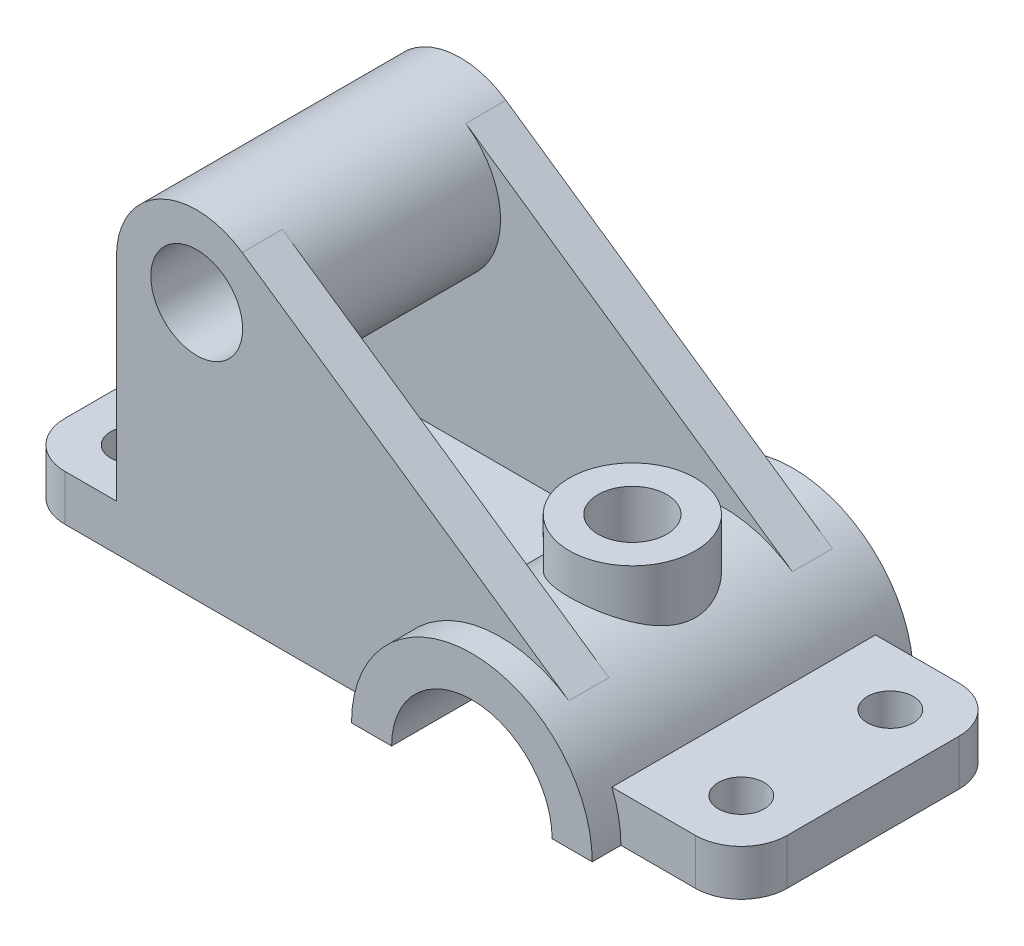
SolidWorks part; units mm, degrees
material "AISI 304"
ref_plane "Front Plane" through (0, 0, 0) normal (0, 0, 1) x (1, 0, 0)
ref_plane "Top Plane" through (0, 0, 0) normal (0, 1, 0) x (1, 0, 0)
ref_plane "Right Plane" through (0, 0, 0) normal (1, 0, 0) x (0, 0, -1)
sketch "Sketch1" plane through (0, 0, 0) normal (0, 1, 0) x (1, 0, 0)
  line L1 (55, -23) -> (-55, -23)
  line L2 (63, -15) -> (63, 15)
  line L3 (55, 23) -> (-55, 23)
  line L4 (-63, -15) -> (-63, 15)
  line L5 (63, -23) -> (-63, 23) construction
  line L6 (63, 23) -> (-63, -23) construction
  line L7 (-53, -13) -> (53, -13) construction
  line L8 (-53, -13) -> (-53, 13) construction
  line L9 (-53, 13) -> (53, 13) construction
  line L10 (53, -13) -> (53, 13) construction
  line L11 (-53, -13) -> (53, 13) construction
  line L12 (-53, 13) -> (53, -13) construction
  arc A0 (-63, -15) -> (-55, -23) centre (-55, -15) ccw
  arc A1 (63, -15) -> (55, -23) centre (55, -15) cw
  arc A2 (63, 15) -> (55, 23) centre (55, 15) ccw
  arc A3 (-55, 23) -> (-63, 15) centre (-55, 15) ccw
  circle A4 centre (-53, 13) radius 4
  circle A5 centre (53, 13) radius 4
  circle A6 centre (-53, -13) radius 4
  circle A7 centre (53, -13) radius 4
  point P0 (0, 0)
  point P18 (0, 0)
  dimension "D3" = 8
  dimension "D6" = 8
  dimension "D1" = 46
  dimension "D2" = 126
  dimension "D4" = 26
  dimension "D5" = 106
extrude "Boss-Extrude1" add sketch "Sketch1" along normal blind 8
sketch "Sketch2" plane through (0, 0, 23) normal (0, 0, 1) x (1, 0, 0)
  line L0 (-55, 0) -> (55, 0) construction
  line L1 (63, 8) -> (63, 0) construction
  line L2 (0, 0) -> (42, 0)
  arc A0 (42, 0) -> (0, 0) centre (21, 0) ccw
  point P4 (63, 4)
  dimension "D1" = 42
  dimension "D2" = 42
extrude "Boss-Extrude2" add sketch "Sketch2" against normal blind 51 and the other way blind 5
sketch "Sketch3" plane through (0, 0, 23) normal (0, 0, 1) x (1, 0, 0)
  line L0 (-46, 45) -> (-46, 0)
  line L1 (0, 0) -> (42, 0)
  line L3 (0, 0) -> (-46, 0)
  line L4 (-24.0593, 56.5302) -> (32.9111, 17.2953)
  arc A1 (-24.0593, 56.5302) -> (-46, 45) centre (-32, 45) ccw
  arc A3 (42, 0) -> (0, 0) centre (21, 0) ccw
  arc A4 (32.9111, 17.2953) -> (0, 0) centre (21, 0) ccw
  dimension "D2" = 14
  dimension "D3" = 45
  dimension "D4" = 67
  dimension "D1" = 0
extrude "Boss-Extrude3" add sketch "Sketch3" against normal blind 7
mirror "Mirror1" about plane through (0, 0, 0) normal (0, 0, 1) of "Boss-Extrude3"
sketch "Sketch7" plane through (0, 0, 16) normal (0, 0, -1) x (-1, 0, 0)
  circle A0 centre (32, 45) radius 14
  arc A1 (46, 45) -> (24.0593, 56.5302) centre (32, 45) ccw construction
extrude "Boss-Extrude5" add sketch "Sketch7" along normal up to next
sketch "Sketch4" plane through (0, 0, 0) normal (0, -1, 0) x (1, 0, 0)
  line L0 (63, 15) -> (63, -15) construction
  circle A0 centre (21, 0) radius 11
  dimension "D1" = 22
  dimension "D2" = 42
extrude "Boss-Extrude4" add sketch "Sketch4" against normal blind 28
sketch "Sketch5" plane through (0, 0, 28) normal (0, 0, 1) x (1, 0, 0)
  line L0 (0, 0) -> (42, 0) construction
  circle A0 centre (21, 0) radius 14
  circle A1 centre (-32, 45) radius 8
  arc A2 (42, 0) -> (0, 0) centre (21, 0) ccw construction
  arc A3 (-24.0593, 56.5302) -> (-46, 45) centre (-32, 45) ccw construction
  dimension "D1" = 28
  dimension "D2" = 16
extrude "Cut-Extrude1" cut sketch "Sketch5" against normal up to next
sketch "Sketch6" plane through (0, 28, 0) normal (0, 1, 0) x (1, 0, 0)
  circle A0 centre (21, 0) radius 6
  dimension "D1" = 12
extrude "Cut-Extrude2" cut sketch "Sketch6" against normal blind 28
